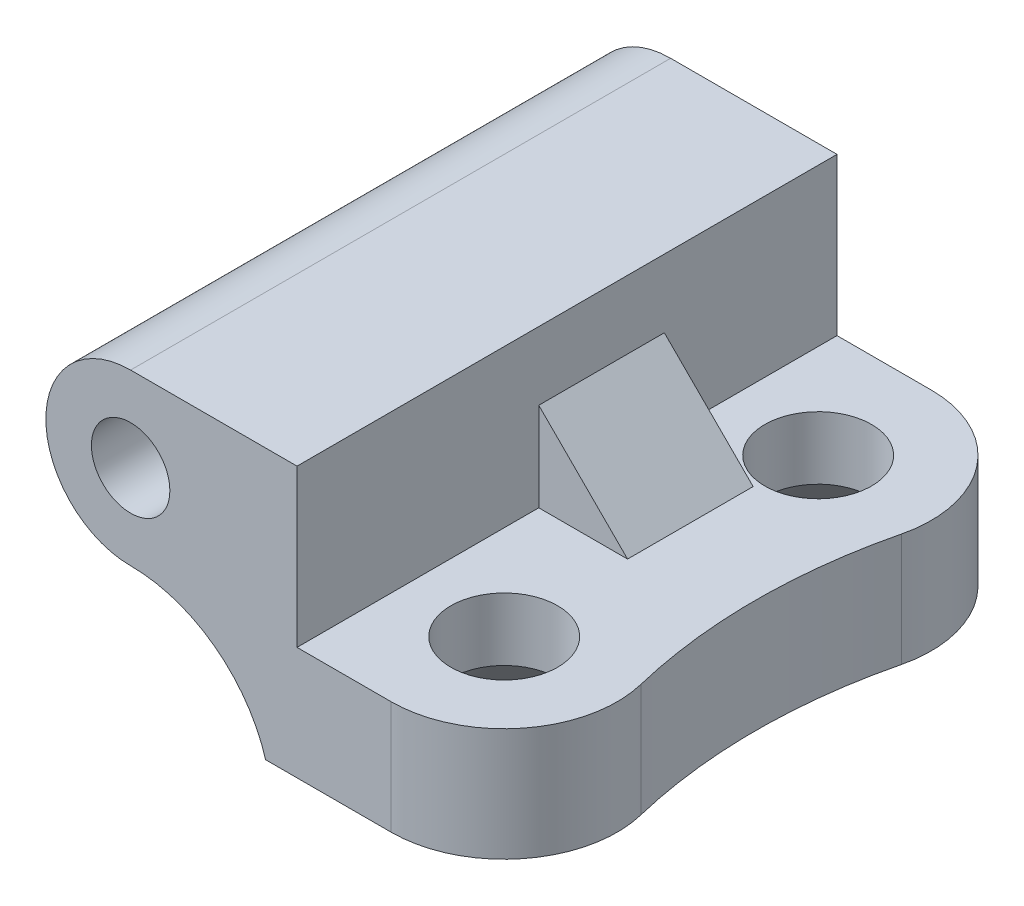
SolidWorks part; units mm, degrees
ref_plane "前视基准面" through (0, 0, 0) normal (0, 0, 1) x (1, 0, 0)
ref_plane "上视基准面" through (0, 0, 0) normal (0, 1, 0) x (1, 0, 0)
ref_plane "右视基准面" through (0, 0, 0) normal (1, 0, 0) x (0, 0, -1)
sketch "草图1" plane through (0, 0, 0) normal (0, 0, 1) x (1, 0, 0)
  line L0 (0, 2.7) -> (5.3, 2.7)
  line L1 (-2.7, 0) -> (-2.7, -2.7) construction
  line L3 (5.3, 2.3) -> (12.8, 2.3) construction
  line L4 (12.8, 2.3) -> (12.8, 5.9) construction
  line L5 (12.8, 5.9) -> (4.3, 5.9) construction
  line L6 (0, 0) -> (13.6453, 0) construction
  line L7 (12.8, -2.3) -> (12.8, -5.9)
  line L8 (12.8, -5.9) -> (4.3, -5.9)
  line L9 (5.3, 2.7) -> (5.3, -2.3)
  line L10 (5.3, -2.3) -> (12.8, -2.3)
  circle A0 centre (0, 0) radius 1.25
  arc A1 (0, 2.7) -> (0, -2.7) centre (0, 0) ccw
  arc A2 (0, 2.7) -> (4.3, 5.9) centre (0, 7.1891) ccw construction
  arc A3 (0, -2.7) -> (4.3, -5.9) centre (0, -7.1891) cw
  dimension "D1" = 2.5
  dimension "D2" = 5.4
  dimension "D9" = 4.4891
  dimension "D3" = 5
  dimension "D4" = 8.5
  dimension "D5" = 7.5
  dimension "D6" = 3.6
  dimension "D7" = 8.5
  dimension "D8" = 3.6
extrude "凸台-拉伸1" add sketch "草图1" along normal blind 17.2
ref_plane "基准面1" through (0, 0, 6) normal (0, 0, 1) x (1, 0, 0)
sketch "草图6" plane through (0, -5.9, 0) normal (0, -1, 0) x (1, 0, 0)
  line L3 (12.8, 0) -> (8.3, 0)
  line L4 (12.8, 17.2) -> (12.8, 0)
  line L5 (12.8, 17.2) -> (8.3, 17.2)
  circle A2 centre (8.3, 13.6) radius 3.6
  circle A4 centre (8.3, 3.6) radius 3.6
  arc A5 (11.7978, 12.7483) -> (11.7978, 4.4517) centre (28.8333, 8.6) ccw
  line M6 (12.8, 17.2) -> (4.3, 17.2)
  line M8 (4.3, 0) -> (12.8, 0)
  line M9 (12.8, 0) -> (12.8, 17.2)
extrude "切除-拉伸1" cut sketch "草图6" against normal through all contours A2 A5 A4 M8 M9 M6
ref_plane "基准面3" through (0, 0, 5.5) normal (0, 0, 1) x (1, 0, 0)
sketch "草图7" plane through (0, 0, 5.5) normal (0, 0, 1) x (1, 0, 0)
  line L2 (8.1284, -2.3) -> (5.3, -2.3)
  line L3 (5.3, -2.3) -> (5.3, 0.5284)
  line L4 (8.1284, -2.3) -> (5.3, 0.5284)
  line L5 (5.3, -2.3) -> (5.3, 2.7) construction
  line L6 (5.3, -2.3) -> (5.3, 2.7) construction
  line L7 (8.3, -2.3) -> (5.3, -2.3) construction
  line L8 (8.3, -2.3) -> (5.3, -2.3) construction
  point P2 (3.5339, -8.9429)
  dimension "D1" = 4
extrude "凸台-拉伸2" add sketch "草图7" along normal blind 4
hole_wizard "打孔尺寸(%根据)开槽半沉头木螺钉的类型1" positions "3D草图1" profile "草图8" countersink size "M3" standard "GB"
sketch3d "3D草图1"
  line L0 (8.3, -2.3, 3.6) -> (8.3, -5.9, 3.6) construction
  line L1 (8.3, -2.3, 13.6) -> (8.3, -5.9, 13.6) construction
  point P0 (8.3, -5.9, 3.6)
  point P4 (8.3, -5.9, 13.6)
sketch "草图8" plane through (8.3, -5.9, 3.6) normal (1, 0, 0) x (0, 0, -1)
  line L0 (0, 0) -> (0, 9.6215)
  line L1 (0, 9.6215) -> (1.7, 8.6)
  line L2 (1.7, 8.6) -> (1.7, 1.6)
  line L3 (1.7, 1.6) -> (3.3, 0)
  line L5 (3.3, 0) -> (0, 0)
  line L6 (-1.7, 1.6) -> (-3.3, 0) construction
  line L10 (0, 9.6215) -> (-1.7, 8.6) construction
  line L11 (0, -6.35) -> (0, 107.95) construction
  dimension "孔直径" = 3.4
  dimension "孔深度" = 8.6
  dimension "近端锥形沉头孔直径" = 6.6
  dimension "近端锥形沉头孔角度" = 90
  dimension "导头角度" = 118
